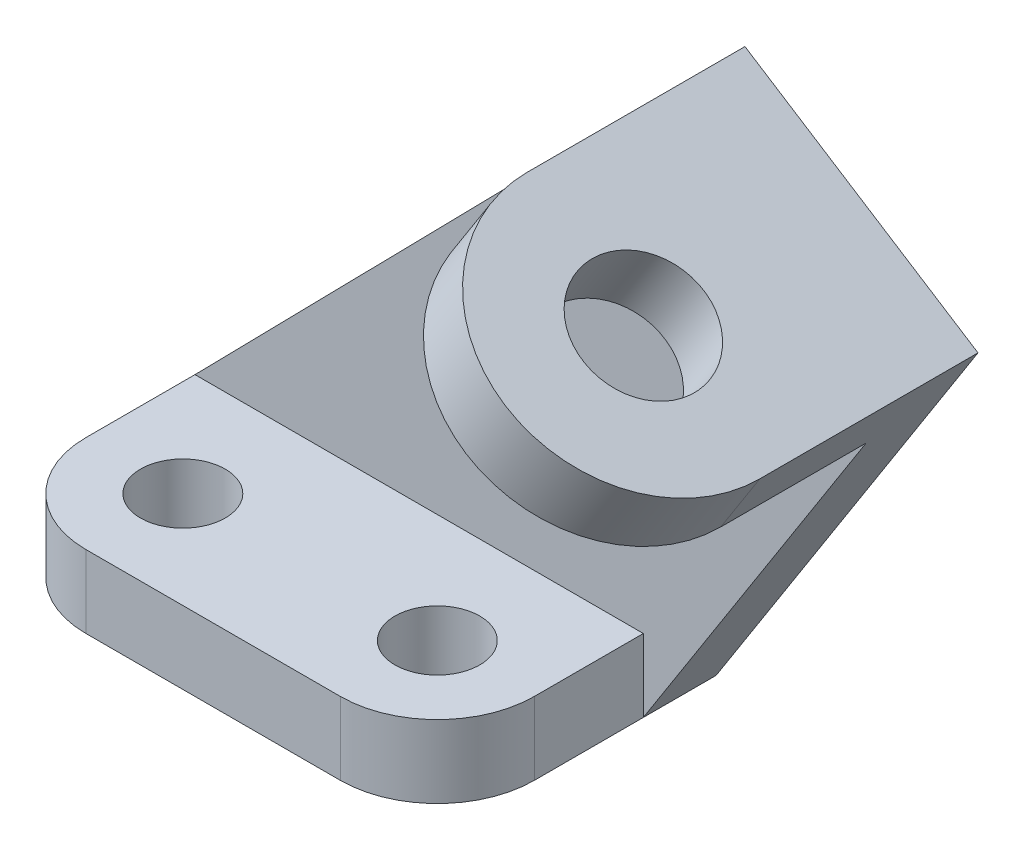
SolidWorks part; units mm, degrees
ref_plane "Front Plane" through (0, 0, 0) normal (0, 0, 1) x (1, 0, 0)
ref_plane "Top Plane" through (0, 0, 0) normal (0, 1, 0) x (1, 0, 0)
ref_plane "Right Plane" through (0, 0, 0) normal (1, 0, 0) x (0, 0, -1)
sketch "Sketch1" plane through (0, 0, 0) normal (0, 1, 0) x (1, 0, 0)
  line L0 (29.3687, 0) -> (-29.3687, 0)
  line L1 (-29.3687, 0) -> (-29.3687, -23.8125)
  line L2 (-16.6687, -36.5125) -> (16.6688, -36.5125)
  line L3 (29.3687, -23.8125) -> (29.3687, 0)
  line L4 (0, 0) -> (0, -36.5125) construction
  arc A0 (-29.3687, -23.8125) -> (-16.6687, -36.5125) centre (-16.6687, -23.8125) ccw
  arc A1 (29.3687, -23.8125) -> (16.6688, -36.5125) centre (16.6687, -23.8125) cw
  circle A2 centre (-16.6687, -23.8125) radius 5.5562
  circle A3 centre (16.6687, -23.8125) radius 5.5562
  point P4 (0, 0)
  dimension "D2" = 25.4
  dimension "D4" = 11.1125
  dimension "D1" = 23.8125
  dimension "D3" = 33.3375
extrude "Boss-Extrude1" add sketch "Sketch1" along normal blind 9.525
sketch "Sketch2" plane through (0, 0, 0) normal (0, 0, -1) x (-1, 0, 0)
  line L0 (-29.3687, 0) -> (-63.6827, 53.7568)
  line L1 (-63.6827, 53.7568) -> (-33.1548, 73.2432)
  line L2 (-33.1548, 73.2432) -> (29.3687, 9.525)
  line L3 (-29.3687, 0) -> (29.3687, 0) construction
  line L8 (-29.3687, 0) -> (29.3687, 0)
  line L9 (29.3687, 0) -> (29.3687, 9.525)
  line L10 (29.3687, 9.525) -> (-29.3687, 9.525)
  line L11 (-29.3687, 9.525) -> (-29.3687, 0)
  line L12 (-29.3687, 0) -> (29.3687, 0)
  line L13 (29.3687, 0) -> (29.3687, 9.525)
  point P3 (-48.4187, 63.5)
  point P9 (-48.4187, 68.1921)
  dimension "D1" = 19.05
  dimension "D2" = 63.5
  dimension "D3" = 0
extrude "Boss-Extrude2" add sketch "Sketch2" against normal blind 9.525
sketch "Sketch4" plane through (42.816, 67.0763, 0) normal (0.538, 0.8429, 0) x (0.8429, -0.538, 0)
  line L0 (-11.4617, 0) -> (-11.4617, -28.575)
  line L2 (24.7553, 0) -> (24.7553, -28.575)
  line L3 (24.7553, -28.575) -> (14.5843, -28.575)
  line L4 (-1.2907, -28.575) -> (-11.4617, -28.575)
  arc A0 (-11.4617, -28.575) -> (24.7553, -28.575) centre (6.6468, -28.575) ccw
  circle A1 centre (6.6468, -28.575) radius 7.9375
  line M5 (24.7553, 0) -> (-11.4617, 0)
  line M6 (-11.4617, 0) -> (-11.4617, -9.525)
  line M7 (-11.4617, -9.525) -> (24.7553, -9.525)
  line M8 (24.7553, -9.525) -> (24.7553, 0)
  dimension "D2" = 15.875
  dimension "D1" = 28.575
extrude "Boss-Extrude3" add sketch "Sketch4" against normal blind 9.525 contours M8 M5 M6 M7 | A1 L4 A0 L3 | A1 L3 L2 L0 L4 M7
